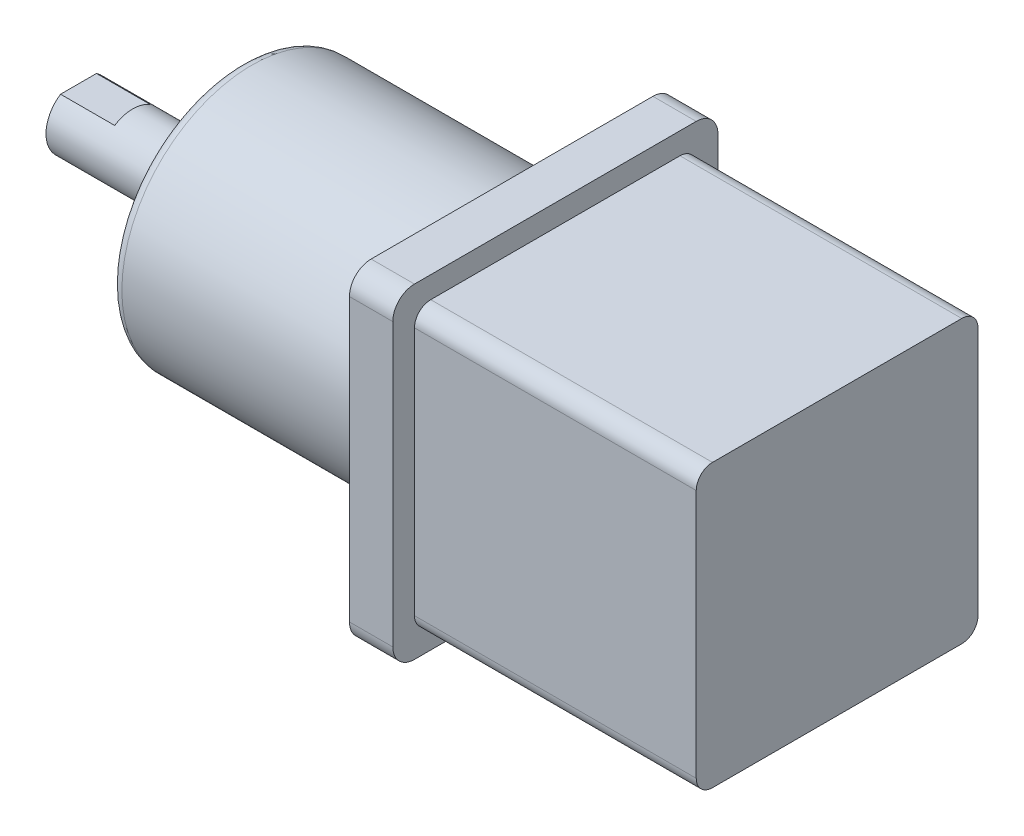
SolidWorks part; units mm, degrees
ref_plane "前视基准面" through (0, 0, 0) normal (0, 0, 1) x (1, 0, 0)
ref_plane "上视基准面" through (0, 0, 0) normal (0, 1, 0) x (1, 0, 0)
ref_plane "右视基准面" through (0, 0, 0) normal (1, 0, 0) x (0, 0, -1)
other "Configuration Table"
sketch "草图1" plane through (0, 0, 0) normal (1, 0, 0) x (0, 0, -1)
  line L1 (15, -15) -> (-15, -15)
  line L2 (15, -15) -> (15, 15)
  line L3 (15, 15) -> (-15, 15)
  line L4 (-15, -15) -> (-15, 15)
  line L5 (15, -15) -> (-15, 15) construction
  line L6 (15, 15) -> (-15, -15) construction
  point P0 (0, 0)
  dimension "D1" = 30
  dimension "D2" = 30
extrude "凸台-拉伸1" add sketch "草图1" along normal blind 30
sketch "草图2" plane through (0, 0, 0) normal (-1, 0, 0) x (0, 0, 1)
  circle A0 centre (0, 0) radius 12
extrude "凸台-拉伸2" add sketch "草图2" along normal blind 25
sketch "草图3" plane through (0, 0, 0) normal (-1, 0, 0) x (0, 0, 1)
  circle A0 centre (0, 0) radius 12 construction
  circle A1 centre (0, 0) radius 12
  circle A2 centre (0, 0) radius 13
extrude "切除-拉伸1" cut sketch "草图3" against normal blind 1
fillet "圆角1" radius 2 4 edges at (15, -15, -15) (15, -15, 15) (15, 15, -15) (15, 15, 15)
fillet "圆角2" radius 1 1 edges at (-25, 0, 12)
sketch "草图4" plane through (-25, 0, 0) normal (-1, 0, 0) x (0, 0, 1)
  circle A0 centre (0, 0) radius 3
sketch "草图5" plane through (30, 0, 0) normal (1, 0, 0) x (0, 0, -1)
  line L0 (-13, 13) -> (13, 13)
  line L1 (-15, 15) -> (15, 15)
  line L2 (-15, 15) -> (-15, -15)
  line L3 (-15, -15) -> (15, -15)
  line L4 (15, 15) -> (15, -15)
  line L5 (13, 13) -> (13, -13)
  line L6 (-13, -13) -> (13, -13)
  line L7 (-13, 13) -> (-13, -13)
  dimension "D1" = 2
extrude "切除-拉伸2" cut sketch "草图5" against normal blind 26
fillet "圆角3" radius 1.5 4 edges at (17, -13, -13) (17, -13, 13) (17, 13, -13) (17, 13, 13)
extrude "凸台-拉伸3" add sketch "草图4" along normal blind 15 contours A0
sketch "草图6" plane through (-40, 0, 0) normal (-1, 0, 0) x (0, 0, 1)
  line L0 (-1.6583, 2.5) -> (1.6583, 2.5)
  line L1 (1.6583, 2.5) -> (1.6583, 3)
  line L2 (1.6583, 3) -> (-1.6583, 3)
  line L3 (-1.6583, 3) -> (-1.6583, 2.5)
  circle A0 centre (0, 0) radius 3 construction
  dimension "D1" = 2.5
  dimension "D2" = 0.5
extrude "切除-拉伸3" cut sketch "草图6" against normal blind 5
